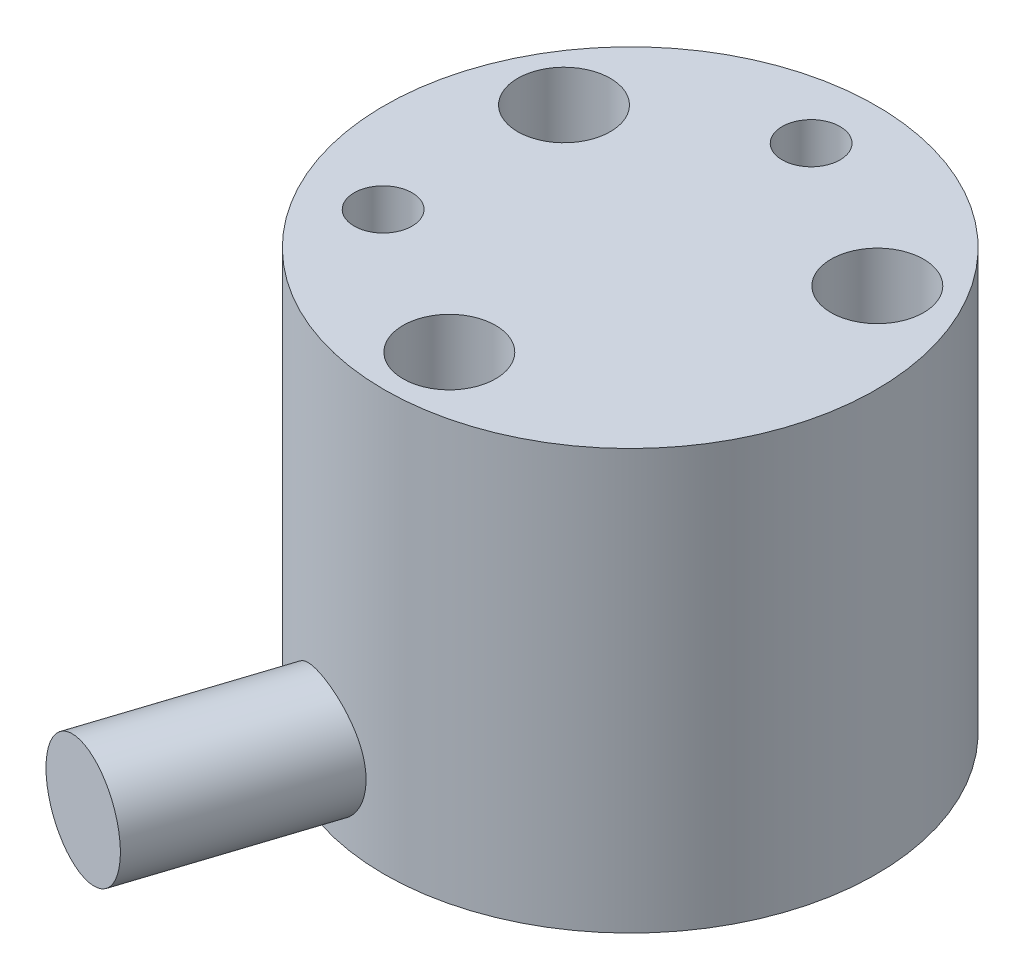
SolidWorks part; units mm, degrees
ref_plane "Front" through (0, 0, 0) normal (0, 0, 1) x (1, 0, 0)
ref_plane "Top" through (0, 0, 0) normal (0, 1, 0) x (1, 0, 0)
ref_plane "Right" through (0, 0, 0) normal (1, 0, 0) x (0, 0, -1)
ref_plane "Plane1" through (0, 0, 0) normal (0, 0, -1) x (-1, 0, 0)
sketch "Sketch1" plane through (0, 0, 0) normal (0, 0, -1) x (-1, 0, 0)
  line L0 (-8.5, 0) -> (0, 0)
  line L1 (0, 0) -> (0, 14.5)
  line L2 (0, 14.5) -> (-8.5, 14.5)
  line L3 (-8.5, 14.5) -> (-8.5, 0)
  line L4 (0, 0) -> (0, 14.5) construction
revolve "Revolve1" add sketch "Sketch1" angle 360 about L4
imported_body "Surface-Imported1"
ref_plane "Plane2" through (-8.4, 0, 0) normal (1, 0, 0) x (0, 0, -1)
sketch "Sketch2" plane through (-8.4, 0, 0) normal (1, 0, 0) x (0, 0, -1)
  line L0 (0.9, 13.234) -> (0.9, 13.2979)
  line L1 (0.9, 13.2979) -> (0.65, 13.2979)
  line L2 (0.65, 13.2979) -> (0.65, 13.5532)
  line L3 (0.65, 13.5532) -> (0.5875, 13.5532)
  line L4 (0.5875, 13.5532) -> (0.5875, 13.2979)
  line L5 (0.5875, 13.2979) -> (0.3375, 13.2979)
  line L6 (0.3375, 13.2979) -> (0.3375, 13.234)
  line L7 (0.3375, 13.234) -> (0.5875, 13.234)
  line L8 (0.5875, 13.234) -> (0.5875, 12.9787)
  line L9 (0.5875, 12.9787) -> (0.65, 12.9787)
  line L10 (0.65, 12.9787) -> (0.65, 13.234)
  line L11 (0.65, 13.234) -> (0.9, 13.234)
extrude "Cut-Extrude1" cut sketch "Sketch2" against normal up to surface
imported_body "Surface-Imported2"
ref_plane "Plane3" through (0, 0, -8.4) normal (0, 0, 1) x (1, 0, 0)
sketch "Sketch3" plane through (0, 0, -8.4) normal (0, 0, 1) x (1, 0, 0)
  line L0 (1, 13.234) -> (1, 13.2979)
  line L1 (1, 13.2979) -> (0.75, 13.2979)
  line L2 (0.75, 13.2979) -> (0.75, 13.5532)
  line L3 (0.75, 13.5532) -> (0.6875, 13.5532)
  line L4 (0.6875, 13.5532) -> (0.6875, 13.2979)
  line L5 (0.6875, 13.2979) -> (0.4375, 13.2979)
  line L6 (0.4375, 13.2979) -> (0.4375, 13.234)
  line L7 (0.4375, 13.234) -> (0.6875, 13.234)
  line L8 (0.6875, 13.234) -> (0.6875, 12.9787)
  line L9 (0.6875, 12.9787) -> (0.75, 12.9787)
  line L10 (0.75, 12.9787) -> (0.75, 13.234)
  line L11 (0.75, 13.234) -> (1, 13.234)
extrude "Cut-Extrude2" cut sketch "Sketch3" against normal up to surface
imported_body "Surface-Imported3"
sketch "Sketch4" plane through (0, 0, -8.4) normal (0, 0, 1) x (1, 0, 0)
  line L0 (-0.875, 12.5) -> (-0.4375, 13.1064)
  line L1 (-0.4375, 13.1064) -> (0, 12.5)
  line L2 (0, 12.5) -> (0.1875, 12.5)
  line L3 (0.1875, 12.5) -> (-0.3437, 13.266)
  line L4 (-0.3437, 13.266) -> (0.1875, 14)
  line L5 (0.1875, 14) -> (0, 14)
  line L6 (0, 14) -> (-0.4375, 13.3936)
  line L7 (-0.4375, 13.3936) -> (-0.875, 14)
  line L8 (-0.875, 14) -> (-1.0625, 14)
  line L9 (-1.0625, 14) -> (-0.5313, 13.266)
  line L10 (-0.5313, 13.266) -> (-1.0625, 12.5)
  line L11 (-1.0625, 12.5) -> (-0.875, 12.5)
extrude "Cut-Extrude3" cut sketch "Sketch4" against normal up to surface
imported_body "Surface-Imported4"
sketch "Sketch5" plane through (-8.4, 0, 0) normal (1, 0, 0) x (0, 0, -1)
  line L0 (-1.1, 14) -> (-0.6, 13.266)
  line L1 (-0.6, 13.266) -> (-0.6, 12.5)
  line L2 (-0.6, 12.5) -> (-0.4125, 12.5)
  line L3 (-0.4125, 12.5) -> (-0.4125, 13.266)
  line L4 (-0.4125, 13.266) -> (0.0875, 14)
  line L5 (0.0875, 14) -> (-0.1, 14)
  line L6 (-0.1, 14) -> (-0.5063, 13.3936)
  line L7 (-0.5063, 13.3936) -> (-0.9125, 14)
  line L8 (-0.9125, 14) -> (-1.1, 14)
extrude "Cut-Extrude4" cut sketch "Sketch5" against normal up to surface
ref_plane "Plane4" through (0, 2.49, 0) normal (0, 1, 0) x (1, 0, 0)
sketch "Sketch6" plane through (0, 2.49, 0) normal (0, 1, 0) x (1, 0, 0)
  line L0 (-6.5374, -13.6478) -> (-4.6353, -14.2658)
  line L1 (-4.6353, -14.2658) -> (-2.5529, -7.857)
  line L2 (-2.5529, -7.857) -> (-4.455, -7.239)
  line L3 (-4.455, -7.239) -> (-6.5374, -13.6478)
  line L4 (-4.6353, -14.2658) -> (-2.5529, -7.857) construction
revolve "Revolve2" add sketch "Sketch6" angle 360 about L4
hole_wizard "Ø2.0 (2) Diameter Hole1" positions "Sketch8" profile "Sketch7" hole size "Ø2.0" standard "ANSI Metric"
sketch "Sketch8" plane through (0, 0, 0) normal (0, -1, 0) x (-1, 0, 0)
  point P0 (1.0853, 6.155)
  point P1 (-5.8731, -2.1376)
sketch "Sketch7" plane through (-1.0853, 0, -6.155) normal (1, 0, 0) x (0, 0, -1)
  line L0 (0, 0) -> (0, 3)
  line L1 (0, 3) -> (1, 3)
  line L2 (1, 3) -> (1, 0)
  line L5 (1, 0) -> (0, 0)
  line L10 (0, 3) -> (-1, 3) construction
  line L11 (0, -6.35) -> (0, 107.95) construction
  dimension "Hole Dia." = 2
  dimension "Hole Depth" = 3
  dimension "Drill Angle" = 180
hole_wizard "Ø2.0 (2) Diameter Hole2" positions "Sketch10" profile "Sketch9" hole size "Ø2.0" standard "ANSI Metric"
sketch "Sketch10" plane through (0, 0, 0) normal (0, -1, 0) x (-1, 0, 0)
  point P0 (6.2262, -0.5447)
  point P1 (-3.5849, -5.1197)
  point P2 (-2.6414, 5.6644)
sketch "Sketch9" plane through (-6.2262, 0, 0.5447) normal (1, 0, 0) x (0, 0, -1)
  line L0 (0, 0) -> (0, 3.5)
  line L1 (0, 3.5) -> (1.6, 3.5)
  line L2 (1.6, 3.5) -> (1.6, 0)
  line L5 (1.6, 0) -> (0, 0)
  line L10 (0, 3.5) -> (-1.6, 3.5) construction
  line L11 (0, -6.35) -> (0, 107.95) construction
  dimension "Hole Dia." = 3.2
  dimension "Hole Depth" = 3.5
  dimension "Drill Angle" = 180
hole_wizard "Ø2.0 (2) Diameter Hole3" positions "Sketch12" profile "Sketch11" hole size "Ø2.0" standard "ANSI Metric"
sketch "Sketch12" plane through (0, 14.5, 0) normal (0, 1, 0) x (1, 0, 0)
  point P0 (0, 6.25)
  point P1 (-5.4127, -3.125)
sketch "Sketch11" plane through (0, 14.5, -6.25) normal (1, 0, 0) x (0, 0, 1)
  line L0 (0, 0) -> (0, 3)
  line L1 (0, 3) -> (1, 3)
  line L2 (1, 3) -> (1, 0)
  line L5 (1, 0) -> (0, 0)
  line L10 (0, 3) -> (-1, 3) construction
  line L11 (0, -6.35) -> (0, 107.95) construction
  dimension "Hole Dia." = 2
  dimension "Hole Depth" = 3
  dimension "Drill Angle" = 180
hole_wizard "Ø2.0 (2) Diameter Hole4" positions "Sketch14" profile "Sketch13" hole size "Ø2.0" standard "ANSI Metric"
sketch "Sketch14" plane through (0, 14.5, 0) normal (0, 1, 0) x (1, 0, 0)
  point P0 (0, -6.25)
  point P1 (5.4127, 3.125)
  point P2 (-5.4127, 3.125)
sketch "Sketch13" plane through (0, 14.5, 6.25) normal (1, 0, 0) x (0, 0, 1)
  line L0 (0, 0) -> (0, 3.5)
  line L1 (0, 3.5) -> (1.6, 3.5)
  line L2 (1.6, 3.5) -> (1.6, 0)
  line L5 (1.6, 0) -> (0, 0)
  line L10 (0, 3.5) -> (-1.6, 3.5) construction
  line L11 (0, -6.35) -> (0, 107.95) construction
  dimension "Hole Dia." = 3.2
  dimension "Hole Depth" = 3.5
  dimension "Drill Angle" = 180
